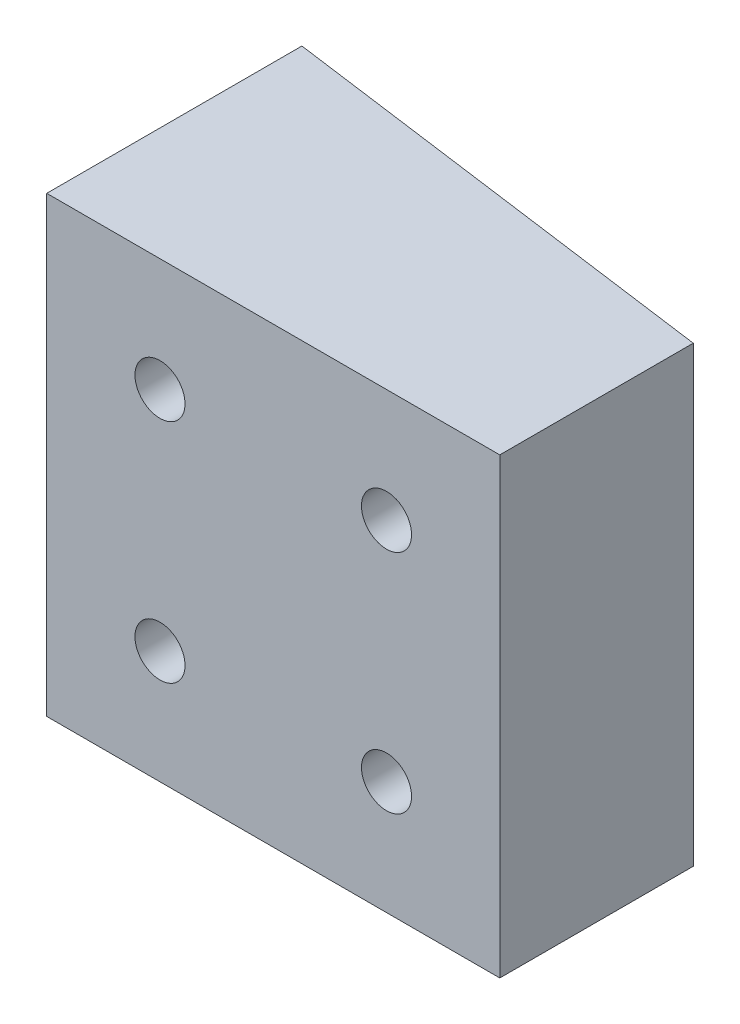
SolidWorks part; units mm, degrees
ref_plane "Front Plane" through (0, 0, 0) normal (0, 0, 1) x (1, 0, 0)
ref_plane "Top Plane" through (0, 0, 0) normal (0, 1, 0) x (1, 0, 0)
ref_plane "Right Plane" through (0, 0, 0) normal (1, 0, 0) x (0, 0, -1)
sketch "Sketch1" plane through (0, 0, 0) normal (0, 1, 0) x (1, 0, 0)
  line L0 (114.3, 0) -> (-152.4, 0) construction
  line L1 (-91.8318, 41.1109) -> (140.9711, 9.4194) construction
  line L2 (50.8, 0) -> (0, 0)
  line L3 (0, 28.6098) -> (50.8, 21.6944)
  line L5 (0, 0) -> (50.8, 0)
  line L6 (0, 0) -> (0, 28.6098)
  line L8 (50.8, 0) -> (50.8, 21.6944)
  dimension "D1" = 50.8
extrude "Boss-Extrude1" add sketch "Sketch1" along normal blind 50.8 contours L2 L8 L3 L6
sketch "Sketch2" plane through (0, 0, 0) normal (0, 0, 1) x (1, 0, 0)
  line L5 (0, 50.8) -> (50.8, 0) construction
  line L6 (0, 0) -> (50.8, 50.8) construction
  line L13 (12.7, 12.7) -> (38.1, 12.7) construction
  line L14 (38.1, 12.7) -> (38.1, 38.1) construction
  line L15 (38.1, 38.1) -> (12.7, 38.1) construction
  line L16 (12.7, 38.1) -> (12.7, 12.7) construction
  dimension "D1" = 25.4
  dimension "D2" = 25.4
hole_wizard "CSK for #10 Flat Head Machine Screw (100)1" positions "Sketch3" profile "Sketch4" countersink size "#10" standard "ANSI Inch" end condition through all
sketch "Sketch3" plane through (320.742, -316.3951, -35.56) normal (0, 0, 1) x (1, 0, 0)
  point P0 (-308.0419, 227.4951)
  point P2 (-308.0419, 252.8951)
  point P4 (-308.042, 329.0951)
  point P6 (-308.042, 354.4951)
sketch "Sketch4" plane through (12.7001, -88.9, -35.56) normal (1, 0, 0) x (0, 1, 0)
  line L0 (0, 0) -> (0, 35.56)
  line L1 (0, 35.56) -> (2.8067, 35.56)
  line L2 (2.8067, 35.56) -> (2.8067, 6.0833)
  line L3 (2.8067, 6.0833) -> (8.89, 0)
  line L4 (8.89, 0) -> (0, 0)
  line L5 (-2.8067, 6.0833) -> (-8.89, 0) construction
  line L6 (0, -6.35) -> (0, 107.95) construction
  dimension "Thru Hole Dia." = 5.6134
  dimension "Thru Hole Depth" = 35.56
  dimension "Near C'Sink Dia." = 17.78
  dimension "Near C'Sink Angle" = 90
hole_wizard "CSK for #10 Flat Head Machine Screw (100)2" positions "Sketch5" profile "Sketch6" countersink size "#10" standard "ANSI Inch" end condition through all
sketch "Sketch5" plane through (320.742, -316.3951, -33.02) normal (0, 0, 1) x (1, 0, 0)
  point P0 (-282.6419, 227.4951)
  point P2 (-282.6419, 252.8951)
  point P4 (-282.642, 329.0951)
  point P6 (-282.642, 354.4951)
sketch "Sketch6" plane through (38.1001, -88.9, -33.02) normal (1, 0, 0) x (0, 1, 0)
  line L0 (0, 0) -> (0, 33.02)
  line L1 (0, 33.02) -> (2.8067, 33.02)
  line L2 (2.8067, 33.02) -> (2.8067, 6.0833)
  line L3 (2.8067, 6.0833) -> (8.89, 0)
  line L4 (8.89, 0) -> (0, 0)
  line L5 (-2.8067, 6.0833) -> (-8.89, 0) construction
  line L6 (0, -6.35) -> (0, 107.95) construction
  dimension "Thru Hole Dia." = 5.6134
  dimension "Thru Hole Depth" = 33.02
  dimension "Near C'Sink Dia." = 17.78
  dimension "Near C'Sink Angle" = 90
